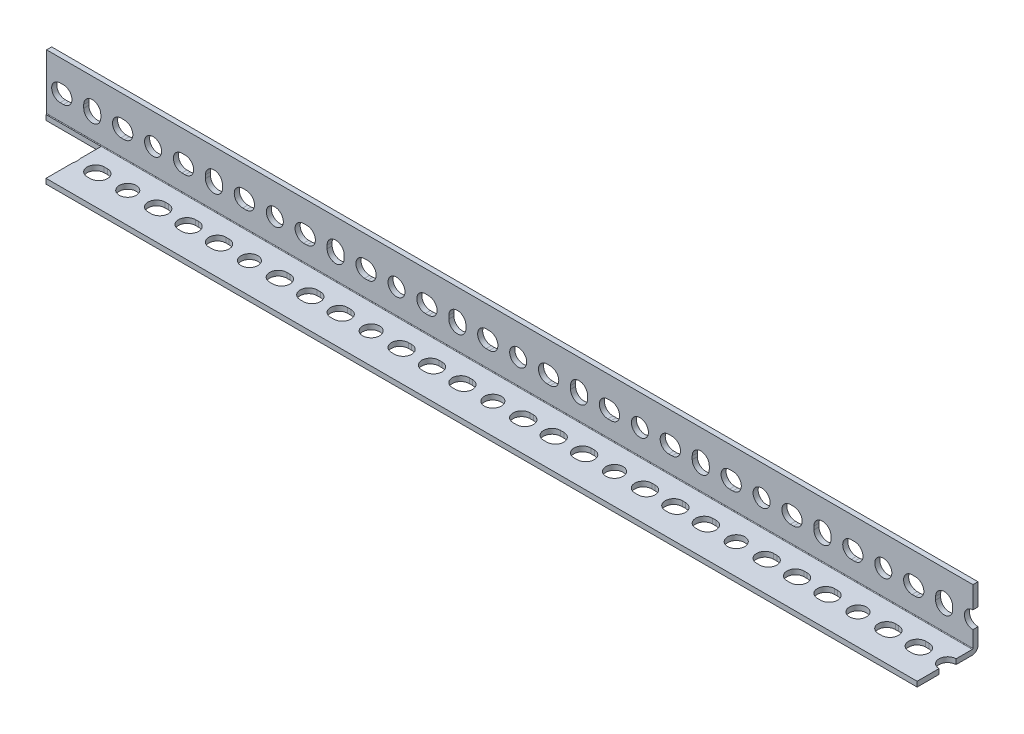
SolidWorks part; units mm, degrees
ref_plane "Front Plane" through (0, 0, 0) normal (0, 0, 1) x (1, 0, 0)
ref_plane "Top Plane" through (0, 0, 0) normal (0, 1, 0) x (1, 0, 0)
ref_plane "Right Plane" through (0, 0, 0) normal (1, 0, 0) x (0, 0, -1)
sketch "Sketch1" plane through (0, 0, 0) normal (1, 0, 0) x (0, 0, -1)
  line L0 (-19.05, -15.875) -> (15.875, -15.875) construction
  line L1 (15.875, -15.875) -> (15.875, 19.05) construction
  line L2 (15.875, 19.05) -> (19.05, 19.05) construction
  line L3 (19.05, 19.05) -> (19.05, -19.05) construction
  line L4 (19.05, -19.05) -> (-19.05, -19.05) construction
  line L5 (-19.05, -19.05) -> (-19.05, -15.875) construction
  line L6 (0, -19.05) -> (0, 19.05) construction
  line L7 (19.05, 0) -> (-19.05, 0) construction
  arc A0 (15.494, -15.875) -> (15.875, -15.494) centre (15.494, -15.494) ccw construction
  dimension "D1" = 0.381
  dimension "Thickness | T" = 3.175
  dimension "Width (B)" = 38.1
  dimension "Width (A)" = 38.1
sketch "Sketch2" plane through (0, 0, 0) normal (0, 0, 1) x (1, 0, 0)
  line L0 (-1219.2, 0) -> (1219.2, 0) construction
  line L1 (-1219.2, 19.05) -> (1219.2, 19.05) construction
  line L2 (-1219.2, 19.05) -> (-1219.2, -19.05) construction
  line L3 (-1219.2, -19.05) -> (1219.2, -19.05) construction
  line L4 (1219.2, 19.05) -> (1219.2, -19.05) construction
  line L5 (0, 19.05) -> (0, -19.05) construction
  line L6 (1191.641, 0) -> (1189.609, 0) construction
  line L7 (-1219.2, -15.875) -> (1219.2, -15.875) construction
  line L8 (1191.641, -5.334) -> (1189.609, -5.334) construction
  line L9 (1191.641, 5.334) -> (1189.609, 5.334) construction
  line L10 (1171.575, -1.016) -> (1171.575, 1.016) construction
  line L11 (1166.241, -1.016) -> (1166.241, 1.016) construction
  line L12 (1176.909, -1.016) -> (1176.909, 1.016) construction
  line L14 (1153.541, 0) -> (1151.509, 0) construction
  line L15 (1153.541, -5.334) -> (1151.509, -5.334) construction
  line L16 (1153.541, 5.334) -> (1151.509, 5.334) construction
  circle A0 centre (1209.675, 0) radius 5.334 construction
  arc A2 (1191.641, -5.334) -> (1191.641, 5.334) centre (1191.641, 0) ccw construction
  arc A3 (1189.609, 5.334) -> (1189.609, -5.334) centre (1189.609, 0) ccw construction
  arc A4 (1166.241, -1.016) -> (1176.909, -1.016) centre (1171.575, -1.016) ccw construction
  arc A5 (1176.909, 1.016) -> (1166.241, 1.016) centre (1171.575, 1.016) ccw construction
  arc A6 (1153.541, -5.334) -> (1153.541, 5.334) centre (1153.541, 0) ccw construction
  arc A7 (1151.509, 5.334) -> (1151.509, -5.334) centre (1151.509, 0) ccw construction
  point P15 (1123.95, 0)
  point P16 (-1123.95, 0)
  point P17 (1190.625, 0)
  point P24 (1215.009, 0)
  point P26 (1171.575, 0)
  point P37 (1152.525, 0)
  dimension "Mounting Hole Diameter" = 10.668
  dimension "Length | L" = 2438.4
  dimension "D1" = 9.525
  dimension "D2" = 85.725
  dimension "D3" = 12.7
  dimension "D4" = 19.05
  dimension "Mounting Hole Center to Center" = 19.05
  dimension "D5" = 19.05
  dimension "D7" = 19.05
sketch "Sketch3" plane through (0, 0, 0) normal (0, 1, 0) x (1, 0, 0)
  line L0 (1191.641, 0) -> (1189.609, 0) construction
  line L1 (-1219.2, 19.05) -> (1219.2, 19.05) construction
  line L2 (-1219.2, 19.05) -> (-1219.2, -19.05) construction
  line L3 (-1219.2, -19.05) -> (1219.2, -19.05) construction
  line L4 (1219.2, 19.05) -> (1219.2, -19.05) construction
  line L5 (-1219.2, 15.875) -> (1219.2, 15.875) construction
  line L6 (1191.641, -5.334) -> (1189.609, -5.334) construction
  line L7 (1170.559, 0) -> (1172.591, 0) construction
  line L8 (1191.641, 5.334) -> (1189.609, 5.334) construction
  line L12 (1151.509, 0) -> (1153.541, 0) construction
  line L13 (1151.509, 5.334) -> (1153.541, 5.334) construction
  line L14 (1151.509, -5.334) -> (1153.541, -5.334) construction
  line L16 (1191.641, 5.334) -> (1209.675, 5.334) construction
  line L17 (1170.559, 5.334) -> (1172.591, 5.334) construction
  line L18 (1170.559, -5.334) -> (1172.591, -5.334) construction
  circle A0 centre (1209.675, 0) radius 5.334 construction
  arc A2 (1191.641, -5.334) -> (1191.641, 5.334) centre (1191.641, 0) ccw construction
  arc A3 (1189.609, 5.334) -> (1189.609, -5.334) centre (1189.609, 0) ccw construction
  arc A6 (1151.509, 5.334) -> (1151.509, -5.334) centre (1151.509, 0) ccw construction
  arc A7 (1153.541, -5.334) -> (1153.541, 5.334) centre (1153.541, 0) ccw construction
  arc A10 (1170.559, 5.334) -> (1170.559, -5.334) centre (1170.559, 0) ccw construction
  arc A11 (1172.591, -5.334) -> (1172.591, 5.334) centre (1172.591, 0) ccw construction
  point P9 (1190.625, 0)
  point P21 (1215.009, 0)
  point P28 (1171.575, 0)
  point P42 (1152.525, 0)
  dimension "D1" = 19.05
sketch "Sketch4" plane through (0, 0, 0) normal (1, 0, 0) x (0, 0, -1)
  line L0 (-19.05, -15.875) -> (15.494, -15.875)
  line L1 (15.875, -15.494) -> (15.875, 19.05)
  line L2 (15.875, 19.05) -> (19.05, 19.05)
  line L3 (19.05, 19.05) -> (19.05, -15.494)
  line L4 (15.494, -19.05) -> (-19.05, -19.05)
  line L5 (-19.05, -19.05) -> (-19.05, -15.875)
  arc A0 (15.494, -15.875) -> (15.875, -15.494) centre (15.494, -15.494) ccw
  arc A1 (19.05, -15.494) -> (15.494, -19.05) centre (15.494, -15.494) cw
extrude "Boss-Extrude1" add sketch "Sketch4" along normal up to vertex (1219.2 mm away) and the other way up to vertex (1219.2 mm away) up to point (1219.2, 0, 0) other way up to point (-1219.2, 0, 0)
sketch "Sketch5" plane through (0, 0, 0) normal (0, 0, 1) x (1, 0, 0)
  line L0 (1189.609, 0) -> (1191.641, 0) construction
  line L1 (1189.609, 5.334) -> (1191.641, 5.334)
  line L2 (1189.609, -5.334) -> (1191.641, -5.334)
  line L3 (1171.575, 1.016) -> (1171.575, -1.016) construction
  line L4 (1176.909, 1.016) -> (1176.909, -1.016)
  line L5 (1166.241, 1.016) -> (1166.241, -1.016)
  line L6 (1151.509, 0) -> (1153.541, 0) construction
  line L7 (1151.509, 5.334) -> (1153.541, 5.334)
  line L8 (1151.509, -5.334) -> (1153.541, -5.334)
  circle A0 centre (1209.675, 0) radius 5.334
  arc A1 (1189.609, 5.334) -> (1189.609, -5.334) centre (1189.609, 0) ccw
  arc A2 (1191.641, -5.334) -> (1191.641, 5.334) centre (1191.641, 0) ccw
  arc A3 (1176.909, 1.016) -> (1166.241, 1.016) centre (1171.575, 1.016) ccw
  arc A4 (1166.241, -1.016) -> (1176.909, -1.016) centre (1171.575, -1.016) ccw
  arc A5 (1151.509, 5.334) -> (1151.509, -5.334) centre (1151.509, 0) ccw
  arc A6 (1153.541, -5.334) -> (1153.541, 5.334) centre (1153.541, 0) ccw
  point P5 (1190.625, 0)
  point P13 (1171.575, 0)
  point P28 (1152.525, 0)
extrude "Cut-Extrude1" cut sketch "Sketch5" against normal through all
pattern_linear "LPattern1" count 33 spacing 76.2 along (-1, 0, 0) of "Cut-Extrude1"
sketch "Sketch6" plane through (0, 0, 0) normal (0, 1, 0) x (1, 0, 0)
  line L0 (1189.609, 0) -> (1191.641, 0) construction
  line L1 (1189.609, 5.334) -> (1191.641, 5.334)
  line L2 (1189.609, -5.334) -> (1191.641, -5.334)
  line L3 (1170.559, 0) -> (1172.591, 0) construction
  line L6 (1151.509, 0) -> (1153.541, 0) construction
  line L7 (1151.509, 5.334) -> (1153.541, 5.334)
  line L8 (1151.509, -5.334) -> (1153.541, -5.334)
  line L11 (1170.559, 5.334) -> (1172.591, 5.334)
  line L12 (1170.559, -5.334) -> (1172.591, -5.334)
  circle A0 centre (1209.675, 0) radius 5.334
  arc A1 (1189.609, 5.334) -> (1189.609, -5.334) centre (1189.609, 0) ccw
  arc A2 (1191.641, -5.334) -> (1191.641, 5.334) centre (1191.641, 0) ccw
  arc A5 (1151.509, 5.334) -> (1151.509, -5.334) centre (1151.509, 0) ccw
  arc A6 (1153.541, -5.334) -> (1153.541, 5.334) centre (1153.541, 0) ccw
  arc A9 (1170.559, 5.334) -> (1170.559, -5.334) centre (1170.559, 0) ccw
  arc A10 (1172.591, -5.334) -> (1172.591, 5.334) centre (1172.591, 0) ccw
  point P8 (1190.625, 0)
  point P15 (1171.575, 0)
  point P22 (1152.525, 0)
extrude "Cut-Extrude2" cut sketch "Sketch6" against normal through all
pattern_linear "LPattern2" count 33 spacing 76.2 along (-1, 0, 0) of "Cut-Extrude2"
sketch "Sketch7" plane through (0, 0, -15.875) normal (0, 0, 1) x (1, 0, 0)
  line L0 (-1219.2, 1.778) -> (1219.2, 1.778) construction
  line L1 (-1219.2, 19.05) -> (-1219.2, -15.494) construction
  line L2 (1219.2, 19.05) -> (1219.2, -15.494) construction
  line L3 (1219.2, -19.05) -> (-1219.2, -19.05) construction
  line L4 (3077.6, 22.606) -> (-639.2, 22.606)
  line L5 (3077.6, 22.606) -> (3077.6, -19.05)
  line L6 (3077.6, -19.05) -> (-639.2, -19.05)
  line L7 (-639.2, 22.606) -> (-639.2, -19.05)
  line L8 (3077.6, 22.606) -> (-639.2, -19.05) construction
  line L9 (3077.6, -19.05) -> (-639.2, 22.606) construction
  dimension "D1" = 3716.8
extrude "Cut-Extrude3" cut sketch "Sketch7" against normal through all both and the other way through all
sketch "Sketch8" plane through (0, -19.05, 0) normal (0, -1, 0) x (1, 0, 0)
  line L0 (-639.2, -15.494) -> (-1219.2, -15.494) construction
  line L1 (-1219.2, 19.05) -> (-1184.656, 19.05)
  line L2 (-1219.2, 19.05) -> (-1219.2, -15.494)
  line L3 (-1219.2, -15.494) -> (-1184.656, -15.494)
  line L4 (-1184.656, 19.05) -> (-1184.656, -15.494)
  dimension "D1" = 34.544
extrude "Cut-Extrude4" cut sketch "Sketch8" against normal through all both and the other way through all
equation "\"D1@Sketch2\"= ( \"Length | L@Sketch2\" - \"Mounting Hole Center to Center@Sketch2\" * \"Num Holes\" ) / 2"
equation "\"Num Holes\"= int ( \"Length | L@Sketch2\" / \"Mounting Hole Center to Center@Sketch2\" ) - 1"
equation "\"D2@Sketch2\"=\"Mounting Hole Center to Center@Sketch2\"*4.5"
equation "\"D3@LPattern1\"=\"Mounting Hole Center to Center@Sketch2\"*4"
equation "\"D4@Sketch2\"=\"Mounting Hole Center to Center@Sketch2\""
equation "\"D3@LPattern2\"=\"Mounting Hole Center to Center@Sketch2\"*4"
equation "\"D7@Sketch2\"=\"Mounting Hole Center to Center@Sketch2\""
